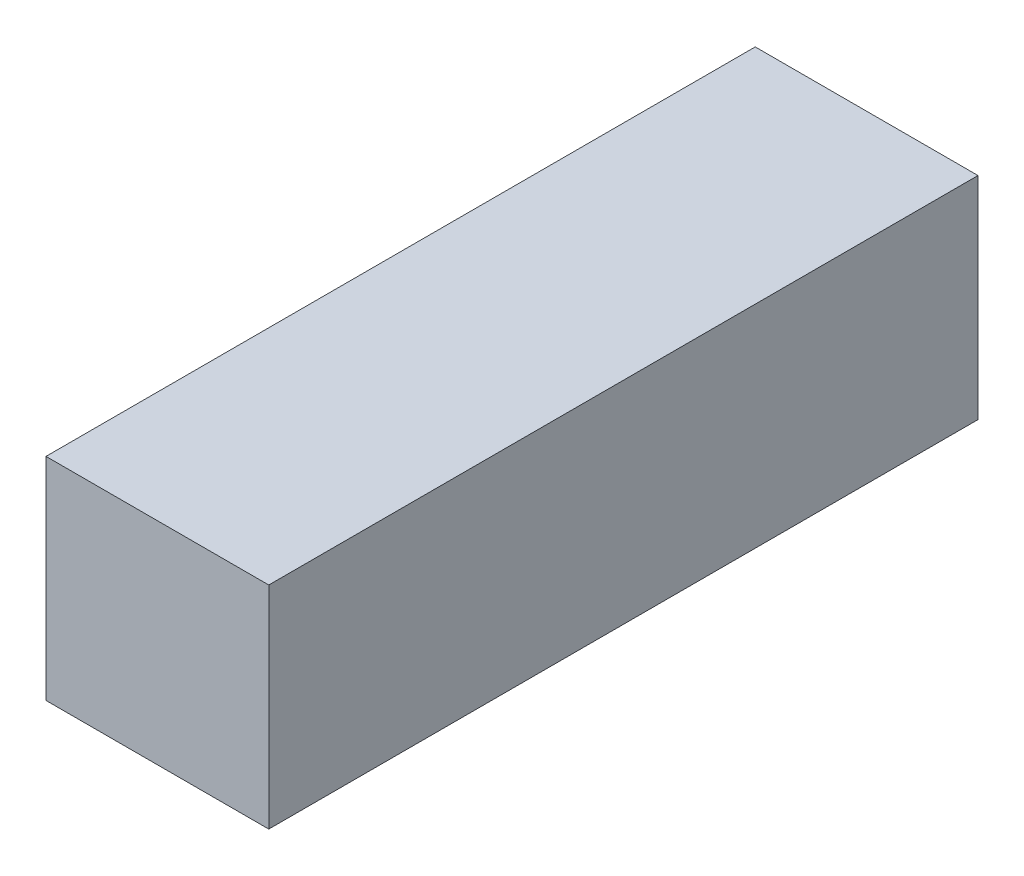
SolidWorks part; units mm, degrees
ref_plane "Front Plane" through (0, 0, 0) normal (0, 0, 1) x (1, 0, 0)
ref_plane "Top Plane" through (0, 0, 0) normal (0, 1, 0) x (1, 0, 0)
ref_plane "Right Plane" through (0, 0, 0) normal (1, 0, 0) x (0, 0, -1)
sketch "Sketch1" plane through (0, 0, 0) normal (0, 0, 1) x (1, 0, 0)
  line L1 (-24.5, -23.25) -> (24.5, -23.25)
  line L2 (-24.5, -23.25) -> (-24.5, 23.25)
  line L3 (-24.5, 23.25) -> (24.5, 23.25)
  line L4 (24.5, -23.25) -> (24.5, 23.25)
  line L5 (-24.5, -23.25) -> (24.5, 23.25) construction
  line L6 (-24.5, 23.25) -> (24.5, -23.25) construction
  point P0 (0, 0)
  dimension "D1" = 49
  dimension "D2" = 46.5
extrude "Boss-Extrude1" add sketch "Sketch1" along normal blind 156
sketch "Sketch2" plane through (0, 0, 156) normal (0, 0, 1) x (1, 0, 0)
  circle A0 centre (0, 0) radius 33.7759
